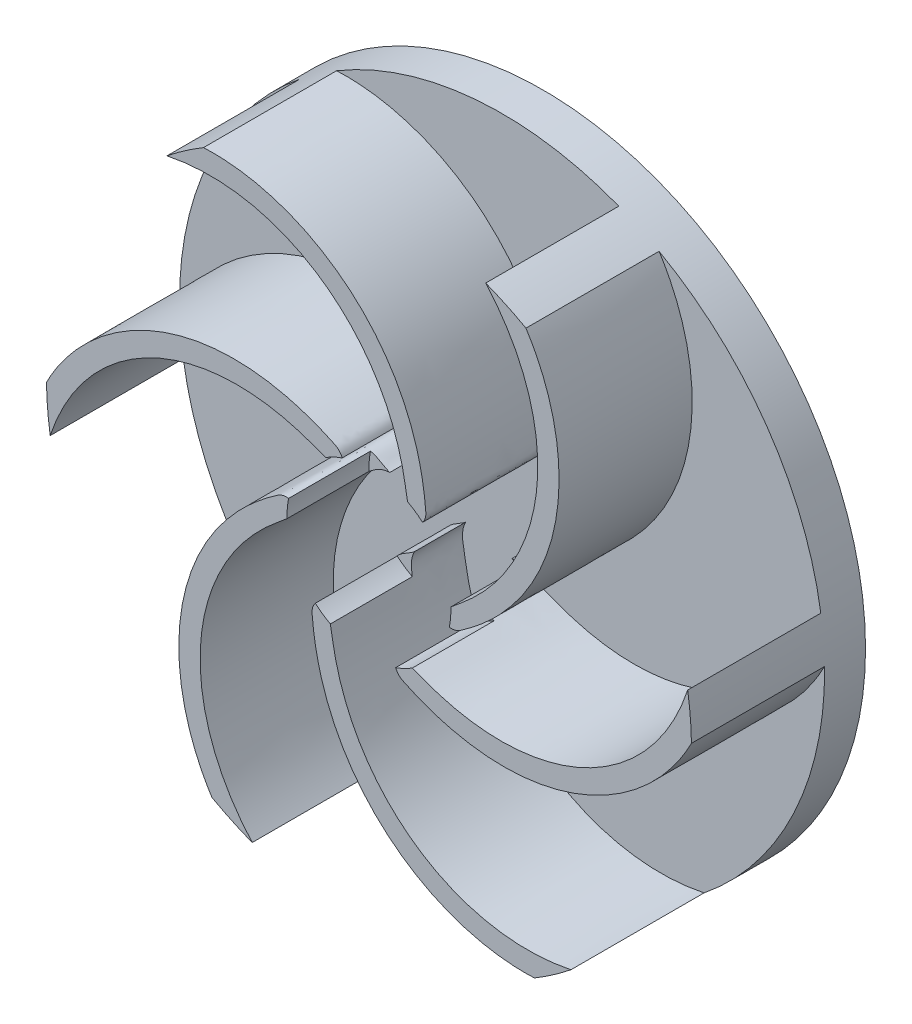
SolidWorks part; units mm, degrees
ref_plane "Front" through (0, 0, 0) normal (0, 0, 1) x (1, 0, 0)
ref_plane "Top" through (0, 0, 0) normal (0, 1, 0) x (1, 0, 0)
ref_plane "Right" through (0, 0, 0) normal (1, 0, 0) x (0, 0, -1)
sketch "Sketch1" plane through (0, 0, 0) normal (0, 0, 1) x (1, 0, 0)
  circle A0 centre (0, 0) radius 31.5
  dimension "D1" = 63
extrude "Extrude1" add sketch "Sketch1" along normal blind 4
sketch "Sketch2" plane through (0, 0, 4) normal (0, 0, 1) x (1, 0, 0)
  line L0 (0, 0) -> (0, 58.241) construction
  line L1 (0, 0) -> (50000, 0) construction
  line L2 (-9, 0) -> (-28.4153, -13.5948) construction
  circle A0 centre (0, 0) radius 9 construction
  circle A1 centre (0, 0) radius 31.5 construction
  arc A3 (-9, 0) -> (-13.4533, -28.4826) centre (2.4715, -16.383) ccw construction
  arc A4 (-8.9107, 1.2648) -> (-15.3351, -27.5152) centre (2.4715, -16.383) ccw
  circle A6 centre (0, 0) radius 31.5 construction
  arc A13 (-8.9225, -1.1786) -> (-11.4031, -29.3636) centre (2.4715, -16.383) ccw
  arc A14 (-9.5736, 0.8192) -> (-14.2496, -29.0876) centre (2.4715, -16.383) ccw construction
  arc A15 (-8.4264, -0.8192) -> (-12.6571, -27.8776) centre (2.4715, -16.383) ccw construction
  arc A16 (-15.3351, -27.5152) -> (-11.4031, -29.3636) centre (0, 0) ccw
  arc A17 (-8.9107, 1.2648) -> (-8.9225, -1.1786) centre (0, 0) ccw
  dimension "D1" = 18
  dimension "D5" = 35
  dimension "D6" = 20
  dimension "D7" = 1
  dimension "D8" = 1
sketch "Sketch8" plane through (0, 0, 4) normal (0, 0, 1) x (1, 0, 0)
  circle A1 centre (0, 0) radius 31.5 construction
  arc A2 (-15.3351, -27.5152) -> (-11.4031, -29.3636) centre (0, 0) ccw
  spline S0 degree 3 poles (-15.3351, -27.5152) (-20.7467, -19.0748) (-19.8609, -6.2433) (-7.7934, 2.0308) (-6.8122, 0.9573) (-5.9638, 0.6583) knots 0 0 0 0 0.907417 0.907417 1 1 1 1
  spline S1 degree 3 poles (-11.4031, -29.3636) (-18.9606, -20.9102) (-18.0571, -8.4773) (-7.8397, -0.161) (-7.1714, 0.6108) (-5.9638, 0.6583) knots 0 0 0 0 0.892041 0.892041 1 1 1 1
  dimension "D1" = 6
extrude "Extrude2" add sketch "Sketch8" along normal blind 13
pattern_circular "CirPattern1" count 6 over 360 about axis through (0, 0, 4) along (0, 0, -1) of "Extrude2"
sketch "Sketch9" plane through (0, 0, 17) normal (0, 0, 1) x (1, 0, 0)
  circle A0 centre (0, 0) radius 8
  dimension "D1" = 16
extrude "Cut-Extrude1" cut sketch "Sketch9" against normal blind 8
